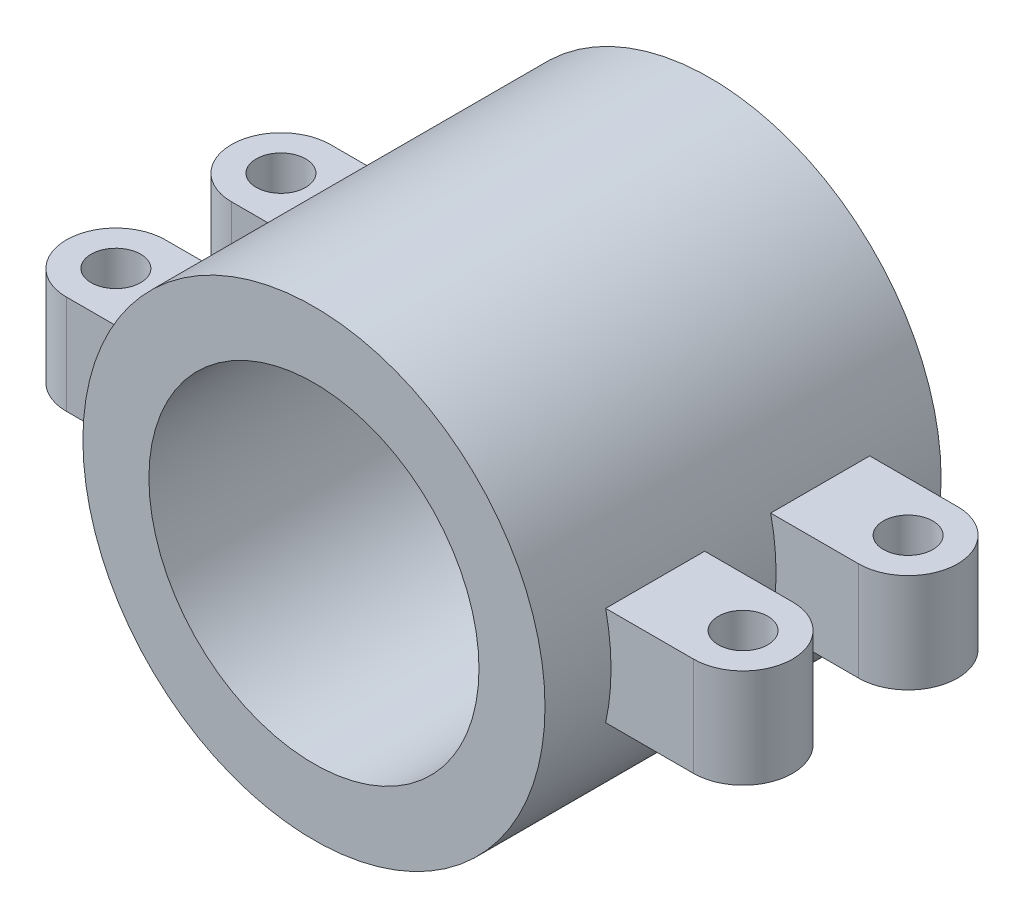
SolidWorks part; units mm, degrees
ref_plane "정면" through (0, 0, 0) normal (0, 0, 1) x (1, 0, 0)
ref_plane "윗면" through (0, 0, 0) normal (0, 1, 0) x (1, 0, 0)
ref_plane "우측면" through (0, 0, 0) normal (1, 0, 0) x (0, 0, -1)
sketch "스케치1" plane through (0, 0, 0) normal (0, 0, 1) x (1, 0, 0)
  circle A0 centre (0, 0) radius 70
  dimension "D1" = 140
extrude "보스-돌출1" add sketch "스케치1" along normal blind 120
sketch "스케치3" plane through (0, 0, 0) normal (0, 0, 1) x (1, 0, 0)
  circle A0 centre (0, 0) radius 50
  dimension "D1" = 100
extrude "컷-돌출1" cut sketch "스케치3" along normal through all
sketch "스케치4" plane through (0, 0, 0) normal (0, 1, 0) x (1, 0, 0)
  line L0 (-95, -35) -> (95, -35) construction
  line L1 (-95, -20) -> (95, -20)
  line L2 (-95, -50) -> (95, -50)
  line L3 (50, 0) -> (-50, 0) construction
  line L4 (-238.592, -60) -> (248.2991, -60) construction
  line L5 (70, 0) -> (-70, 0) construction
  line L6 (-95, -85) -> (95, -85) construction
  line L7 (-95, -100) -> (95, -100)
  line L8 (-95, -70) -> (95, -70)
  arc A0 (-95, -20) -> (-95, -50) centre (-95, -35) ccw
  arc A1 (95, -50) -> (95, -20) centre (95, -35) ccw
  arc A2 (-95, -100) -> (-95, -70) centre (-95, -85) cw
  arc A3 (95, -70) -> (95, -100) centre (95, -85) cw
  point P2 (0, -35)
  point P12 (0, -85)
  dimension "D1" = 15
  dimension "D2" = 20
  dimension "D3" = 95
  dimension "D4" = 0
  dimension "D5" = 60
extrude "보스-돌출2" add sketch "스케치4" along normal mid plane 30
sketch "스케치5" plane through (0, 0, 0) normal (0, 1, 0) x (1, 0, 0)
  circle A0 centre (95, -35) radius 7.5
  arc A1 (95, -50) -> (95, -20) centre (95, -35) ccw construction
  circle A2 centre (95, -85) radius 7.5
  arc A3 (95, -100) -> (95, -70) centre (95, -85) ccw construction
  circle A4 centre (-95, -35) radius 7.5
  circle A5 centre (-95, -85) radius 7.5
  arc A6 (-95, -20) -> (-95, -50) centre (-95, -35) ccw construction
  arc A7 (-95, -70) -> (-95, -100) centre (-95, -85) ccw construction
  point P2 (0, 0)
  dimension "D1" = 15
  dimension "D2" = 15
  dimension "D3" = 15
  dimension "D4" = 15
extrude "컷-돌출2" cut sketch "스케치5" against normal through all both and the other way through all
sketch "스케치6" plane through (0, 0, 0) normal (0, 0, 1) x (1, 0, 0)
  circle A0 centre (0, 0) radius 50
  dimension "D1" = 100
extrude "컷-돌출3" cut sketch "스케치6" along normal through all
